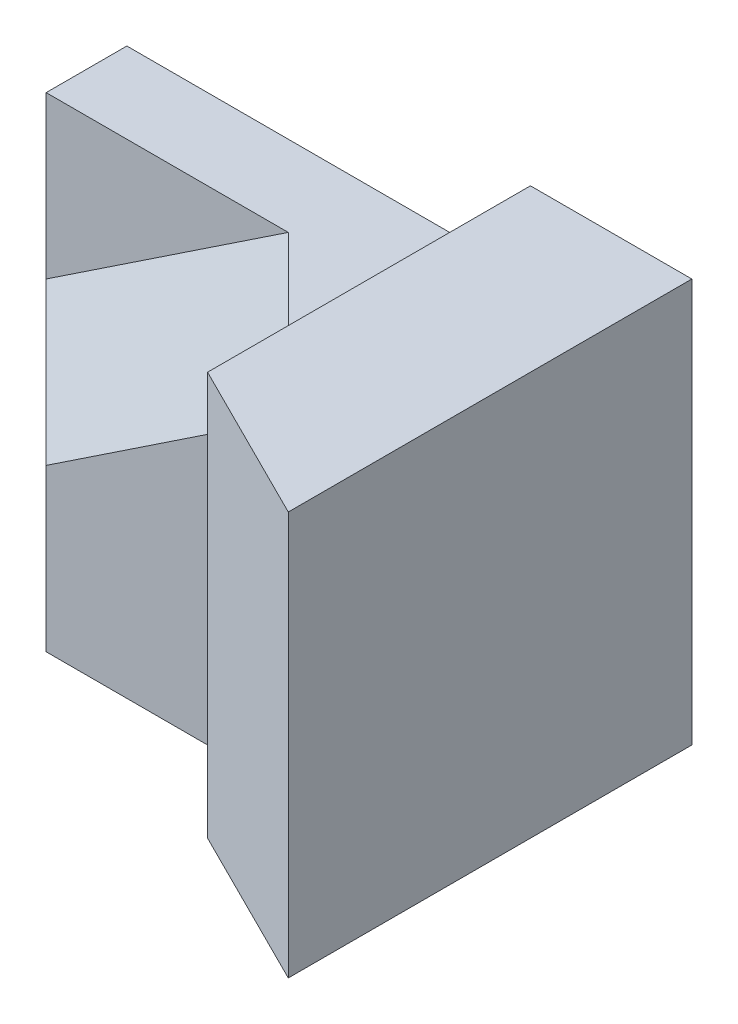
SolidWorks part; units mm, degrees
ref_plane "Front Plane" through (0, 0, 0) normal (0, 0, 1) x (1, 0, 0)
ref_plane "Top Plane" through (0, 0, 0) normal (0, 1, 0) x (1, 0, 0)
ref_plane "Right Plane" through (0, 0, 0) normal (1, 0, 0) x (0, 0, -1)
sketch "Sketch1" plane through (0, 0, 0) normal (0, 0, 1) x (1, 0, 0)
  line L1 (0, 0) -> (70, 0)
  line L2 (0, 0) -> (0, 50)
  line L3 (0, 50) -> (70, 50)
  line L4 (70, 0) -> (70, 50)
  dimension "D1" = 70
  dimension "D2" = 50
extrude "Boss-Extrude1" add sketch "Sketch1" along normal blind 50
sketch "Sketch2" plane through (0, 0, 50) normal (0, 0, 1) x (1, 0, 0)
  line L1 (0, 50) -> (50, 50)
  line L2 (0, 50) -> (0, 40)
  line L3 (0, 40) -> (50, 40)
  line L4 (50, 50) -> (50, 40)
  dimension "D1" = 10
  dimension "D2" = 50
extrude "Cut-Extrude1" cut sketch "Sketch2" against normal blind 50
sketch "Sketch3" plane through (0, 0, 50) normal (0, 0, 1) x (1, 0, 0)
  line L0 (0, 0) -> (70, 0) construction
  line L1 (0, 40) -> (50, 40)
  line L2 (0, 40) -> (0, 0)
  line L3 (0, 0) -> (50, 0)
  line L4 (50, 40) -> (50, 0)
  dimension "D1" = 50
extrude "Cut-Extrude2" cut sketch "Sketch3" against normal blind 40
sketch "Sketch8" plane through (0, 0, 10) normal (0, 0, 1) x (1, 0, 0)
  line L0 (30, 40) -> (0, 20)
  line L1 (0, 20) -> (20, 20)
  line L2 (50, 40) -> (0, 40) construction
  line L3 (30, 40) -> (50, 40)
  line L4 (50, 40) -> (20, 20)
  dimension "D1" = 30
  dimension "D2" = 20
  dimension "D3" = 0
  dimension "D4" = 36.0555
  dimension "D5" = 20
extrude "Cut-Extrude6" cut sketch "Sketch8" against normal blind 20
sketch "Sketch9" plane through (0, 0, 10) normal (0, 0, 1) x (1, 0, 0)
  line L0 (50, 40) -> (20, 20)
  line L1 (20, 20) -> (20, 0)
  line L2 (0, 0) -> (50, 0) construction
  line L3 (20, 0) -> (50, 0)
  line L4 (50, 0) -> (50, 40)
extrude "Boss-Extrude9" add sketch "Sketch9" along normal blind 20
ref_plane "Plane1" through (-9.4118, 14.1176, 9.4118) normal (-0.4851, 0.7276, 0.4851) x (0.8745, 0.4036, 0.2691)
sketch "Sketch10" plane through (-9.4118, 14.1176, 9.4118) normal (-0.4851, 0.7276, 0.4851) x (0.8745, 0.4036, 0.2691)
  line L0 (45.0691, 13.8675) -> (67.94, -2.7735)
  line L1 (67.94, -2.7735) -> (33.6336, -13.8675)
  line L2 (33.6336, -13.8675) -> (10.7628, 2.7735)
  line L3 (10.7628, 2.7735) -> (45.0691, 13.8675)
extrude "Boss-Extrude10" add sketch "Sketch10" against normal blind 20
sketch "Sketch11" plane through (20, 0, 0) normal (-1, 0, 0) x (0, 0, 1)
  line L1 (30, 0) -> (10, 0)
  line L2 (30, 0) -> (30, 20)
  line L3 (30, 20) -> (10, 20)
  line L4 (10, 0) -> (10, 20)
  dimension "D1" = 20
  dimension "D2" = 20
extrude "Cut-Extrude7" cut sketch "Sketch11" along normal blind 20
sketch "Sketch12" plane through (0, 0, 0) normal (0, 0, -1) x (-1, 0, 0)
  line L0 (-50, 40) -> (-20, 20)
  line L1 (-20, 20) -> (0, 20)
  line L2 (0, 20) -> (-30, 40)
  line L3 (-30, 40) -> (-50, 40)
extrude "Boss-Extrude12" add sketch "Sketch12" against normal blind 10
sketch "Sketch13" plane through (0, 40, 0) normal (0, 1, 0) x (1, 0, 0)
  line L0 (30, -10) -> (50, -10)
  line L1 (50, -10) -> (50, -30)
  line L2 (50, -30) -> (30, -10)
extrude "Boss-Extrude13" add sketch "Sketch13" against normal blind 10
sketch "Sketch14" plane through (0, 50, 0) normal (0, 1, 0) x (1, 0, 0)
  line L0 (70, -50) -> (50, -40)
  line L1 (50, 0) -> (50, -50) construction
  line L2 (50, -40) -> (50, -50)
  line L3 (50, -50) -> (70, -50)
  dimension "D1" = 10
extrude "Cut-Extrude8" cut sketch "Sketch14" against normal blind 68
